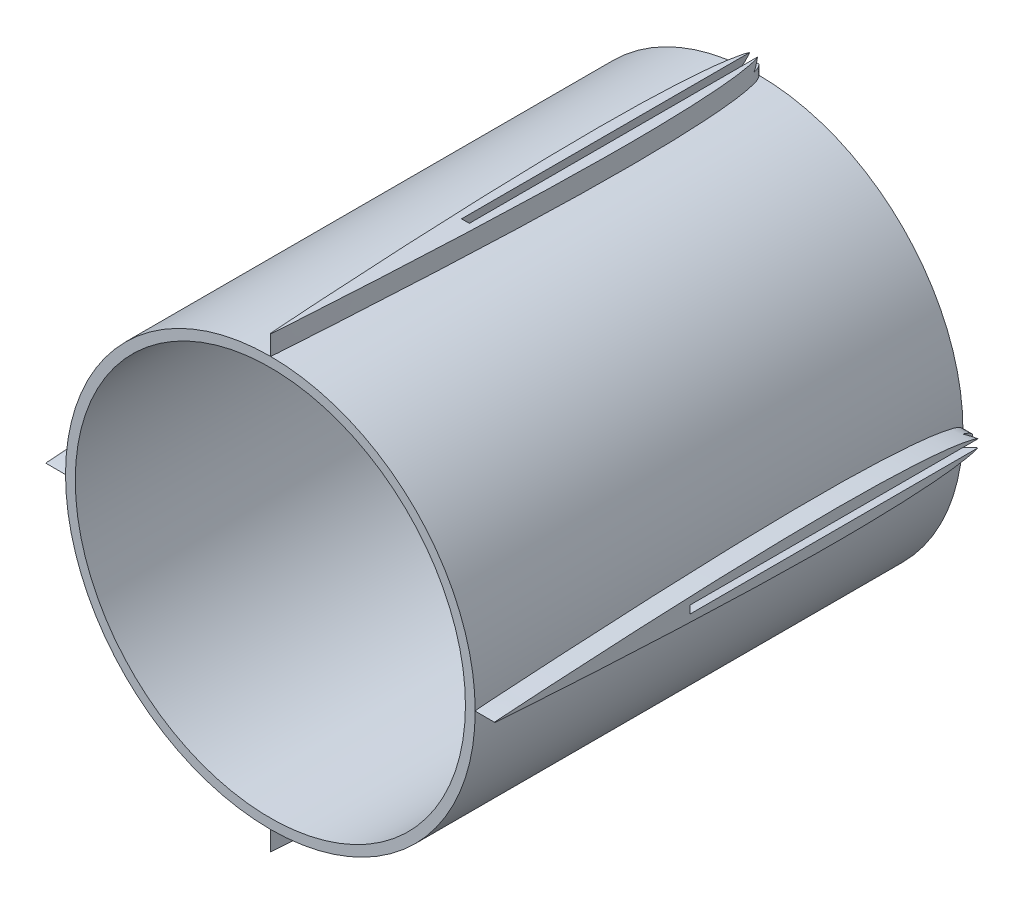
SolidWorks part; units mm, degrees
ref_plane "Front Plane" through (0, 0, 0) normal (0, 0, 1) x (1, 0, 0)
ref_plane "Top Plane" through (0, 0, 0) normal (0, 1, 0) x (1, 0, 0)
ref_plane "Right Plane" through (0, 0, 0) normal (1, 0, 0) x (0, 0, -1)
sketch "Sketch2" plane through (0, 0, 0) normal (0, 0, 1) x (1, 0, 0)
  circle A0 centre (0, 0) radius 20
  circle A1 centre (0, 0) radius 21
  dimension "D1" = 40
  dimension "D2" = 1
extrude "Boss-Extrude1" add sketch "Sketch2" along normal blind 50
curve "Curve2"
  spline degree 3 poles (-0.2116, 0, 47.1255) (0, 0, 51.4381) (0.2116, 0, 47.1255) (0.412, 0, 44.384) (0.6632, 0, 39.9273) (0.9211, 0, 35.0205) (1.1481, 0, 29.9956) (1.3323, 0, 25.0023) (1.4637, 0, 20.0003) (1.5096, 0, 15.8335) (1.4915, 0, 12.4997) (1.4421, 0, 9.9995) (1.347, 0, 7.4978) (1.2148, 0, 5.4158) (1.0548, 0, 3.7454) (0.904, 0, 2.5039) (0.6963, 0, 1.4218) (0.5125, 0, 0.6286) (0, 0, -0.3436) (-0.5125, 0, 0.6286) (-0.6963, 0, 1.4218) (-0.904, 0, 2.5039) (-1.0548, 0, 3.7454) (-1.2148, 0, 5.4158) (-1.347, 0, 7.4978) (-1.4421, 0, 9.9995) (-1.4915, 0, 12.4997) (-1.5096, 0, 15.8335) (-1.4637, 0, 20.0003) (-1.3323, 0, 25.0023) (-1.1481, 0, 29.9956) (-0.9211, 0, 35.0205) (-0.6632, 0, 39.9273) (-0.412, 0, 44.384) (-0.2116, 0, 47.1255) (0, 0, 51.4381) (0.2116, 0, 47.1255) knots -0.099682 -0.049864 -0.024947 0 0.024947 0.049864 0.099682 0.149481 0.199263 0.249028 0.298776 0.348511 0.373377 0.398248 0.423133 0.448054 0.460545 0.473081 0.485732 0.492201 0.5 0.507799 0.514268 0.526919 0.539455 0.551946 0.576867 0.601752 0.626623 0.651489 0.701224 0.750972 0.800737 0.850519 0.900318 0.950136 0.975053 1 1.024947 1.049864 1.099682 periodic
sketch "Sketch4" plane through (0, 0, 0) normal (0, 1, 0) x (1, 0, 0)
  spline S0 degree 3 poles (-0.2116, -47.1255) (0, -51.4381) (0.2116, -47.1255) (0.412, -44.384) (0.6632, -39.9273) (0.9211, -35.0205) (1.1481, -29.9956) (1.3323, -25.0023) (1.4637, -20.0003) (1.5096, -15.8335) (1.4915, -12.4997) (1.4421, -9.9995) (1.347, -7.4978) (1.2148, -5.4158) (1.0548, -3.7454) (0.904, -2.5039) (0.6963, -1.4218) (0.5125, -0.6286) (0, 0.3436) (-0.5125, -0.6286) (-0.6963, -1.4218) (-0.904, -2.5039) (-1.0548, -3.7454) (-1.2148, -5.4158) (-1.347, -7.4978) (-1.4421, -9.9995) (-1.4915, -12.4997) (-1.5096, -15.8335) (-1.4637, -20.0003) (-1.3323, -25.0023) (-1.1481, -29.9956) (-0.9211, -35.0205) (-0.6632, -39.9273) (-0.412, -44.384) (-0.2116, -47.1255) (0, -51.4381) (0.2116, -47.1255) knots -0.099682 -0.049864 -0.024947 0 0.024947 0.049864 0.099682 0.149481 0.199263 0.249028 0.298776 0.348511 0.373377 0.398248 0.423133 0.448054 0.460545 0.473081 0.485732 0.492201 0.5 0.507799 0.514268 0.526919 0.539455 0.551946 0.576867 0.601752 0.626623 0.651489 0.701224 0.750972 0.800737 0.850519 0.900318 0.950136 0.975053 1 1.024947 1.049864 1.099682 only from (0, -50) to (0, -50) construction
  spline S1 degree 3 poles (-0.2116, -47.1255) (0, -51.4381) (0.2116, -47.1255) (0.412, -44.384) (0.6632, -39.9273) (0.9211, -35.0205) (1.1481, -29.9956) (1.3323, -25.0023) (1.4637, -20.0003) (1.5096, -15.8335) (1.4915, -12.4997) (1.4421, -9.9995) (1.347, -7.4978) (1.2148, -5.4158) (1.0548, -3.7454) (0.904, -2.5039) (0.6963, -1.4218) (0.5125, -0.6286) (0, 0.3436) (-0.5125, -0.6286) (-0.6963, -1.4218) (-0.904, -2.5039) (-1.0548, -3.7454) (-1.2148, -5.4158) (-1.347, -7.4978) (-1.4421, -9.9995) (-1.4915, -12.4997) (-1.5096, -15.8335) (-1.4637, -20.0003) (-1.3323, -25.0023) (-1.1481, -29.9956) (-0.9211, -35.0205) (-0.6632, -39.9273) (-0.412, -44.384) (-0.2116, -47.1255) (0, -51.4381) (0.2116, -47.1255) knots -0.099682 -0.049864 -0.024947 0 0.024947 0.049864 0.099682 0.149481 0.199263 0.249028 0.298776 0.348511 0.373377 0.398248 0.423133 0.448054 0.460545 0.473081 0.485732 0.492201 0.5 0.507799 0.514268 0.526919 0.539455 0.551946 0.576867 0.601752 0.626623 0.651489 0.701224 0.750972 0.800737 0.850519 0.900318 0.950136 0.975053 1 1.024947 1.049864 1.099682 only from (0, -50) to (0, -50)
extrude "Boss-Extrude2" add sketch "Sketch4" against normal blind 2.5 from offset 23
sketch "Sketch5" plane through (0, 0, 0) normal (0, 0, -1) x (-1, 0, 0)
  line L0 (0, 0) -> (0, 23) construction
  line L1 (1.5005, 23) -> (-1.5005, 23) construction
  line L2 (-0.4, 23) -> (0.4, 23)
  line L3 (-0.6, 22) -> (0.6, 22)
  line L4 (-0.4, 23) -> (-0.6, 22)
  line L5 (0.6, 22) -> (0.4, 23)
  point P8 (0, 23)
  point P11 (0, 22)
  dimension "D1" = 0.8
  dimension "D2" = 1.2
  dimension "D3" = 1
extrude "Cut-Extrude1" cut sketch "Sketch5" against normal blind 30
pattern_circular "CirPattern1" count 4 over 360 about axis through (0, 0, 50) along (0, 0, -1) of "Cut-Extrude1", "Boss-Extrude2"
